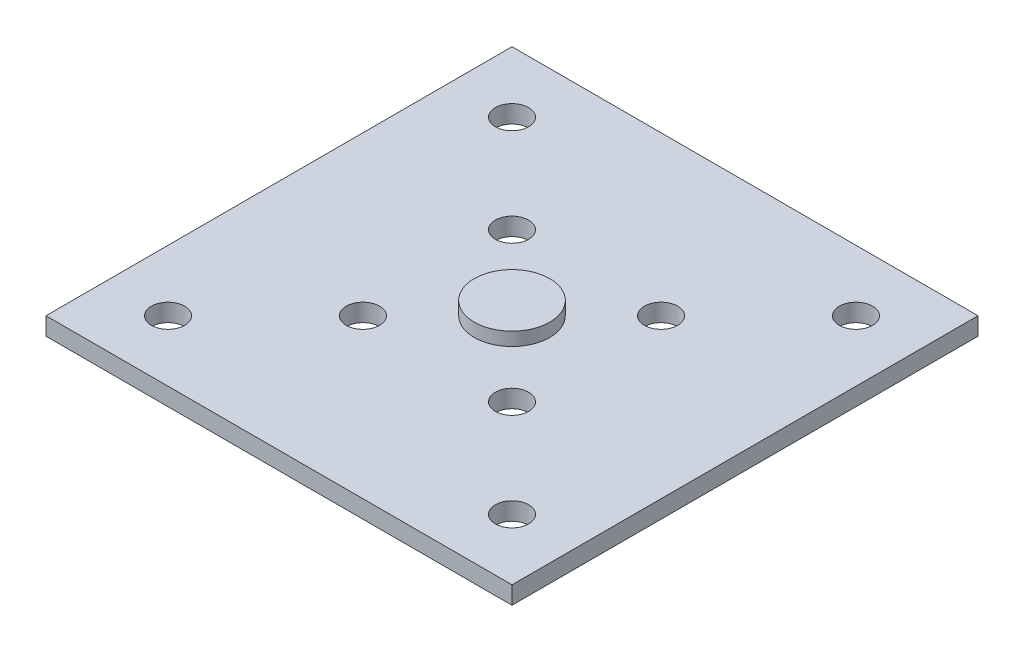
SolidWorks part; units mm, degrees
ref_plane "前视基准面" through (0, 0, 0) normal (0, 0, 1) x (1, 0, 0)
ref_plane "上视基准面" through (0, 0, 0) normal (0, 1, 0) x (1, 0, 0)
ref_plane "右视基准面" through (0, 0, 0) normal (1, 0, 0) x (0, 0, -1)
sketch "草图1" plane through (0, 0, 0) normal (0, 1, 0) x (1, 0, 0)
  line L1 (0, 0) -> (42, 0)
  line L2 (0, 0) -> (0, 42)
  line L3 (0, 42) -> (42, 42)
  line L4 (42, 0) -> (42, 42)
  dimension "D1" = 42
  dimension "D2" = 42
extrude "凸台-拉伸1" add sketch "草图1" along normal blind 1.6
sketch "草图2" plane through (0, 1.6, 0) normal (0, 1, 0) x (1, 0, 0)
  line L0 (42, 42) -> (0, 42) construction
  line L1 (42, 0) -> (42, 42) construction
  line L2 (0, 0) -> (42, 0) construction
  line L3 (0, 42) -> (0, 0) construction
  circle A0 centre (5.5, 36.5) radius 1.5
  circle A1 centre (36.5, 36.5) radius 1.5
  circle A2 centre (5.5, 5.5) radius 1.5
  circle A3 centre (36.5, 5.5) radius 1.5
  point P10 (21, 42)
  point P13 (42, 21)
  point P16 (21, 0)
  point P19 (0, 21)
  dimension "D1" = 3
  dimension "D2" = 3
  dimension "D3" = 3
  dimension "D4" = 3
  dimension "D5" = 15.5
  dimension "D6" = 15.5
  dimension "D8" = 15.5
  dimension "D9" = 15.5
  dimension "D10" = 15.5
  dimension "D11" = 15.5
  dimension "D12" = 15.5
  dimension "D7" = 15.5
extrude "切除-拉伸1" cut sketch "草图2" against normal through all
sketch "草图3" plane through (0, 1.6, 0) normal (0, 1, 0) x (1, 0, 0)
  line L0 (0, 42) -> (0, 0) construction
  line L1 (42, 42) -> (0, 42) construction
  circle A0 centre (21, 21) radius 3.4
  dimension "D1" = 6.8
  dimension "D2" = 21
  dimension "D3" = 21
extrude "凸台-拉伸2" add sketch "草图3" along normal blind 1.2
sketch "草图4" plane through (0, 1.6, 0) normal (0, 1, 0) x (1, 0, 0)
  line L0 (14.2825, 27.7175) -> (21, 21) construction
  line L1 (0, 42) -> (0, 0) construction
  circle A0 centre (14.2825, 27.7175) radius 1.5
  circle A1 centre (27.7175, 27.7175) radius 1.5
  circle A2 centre (14.2825, 14.2825) radius 1.5
  circle A3 centre (27.7175, 14.2825) radius 1.5
  circle A4 centre (21, 21) radius 3.4 construction
  circle A5 centre (21, 21) radius 3.4 construction
  dimension "D1" = 9.5
  dimension "D2" = 9.5
  dimension "D3" = 9.5
  dimension "D4" = 9.5
  dimension "D5" = 3
  dimension "D6" = 3
  dimension "D7" = 3
  dimension "D8" = 3
  dimension "D9" = 45
  dimension "D10" = 0
  dimension "D11" = 9.5
  dimension "D12" = 9.5
extrude "切除-拉伸2" cut sketch "草图4" against normal blind 10
